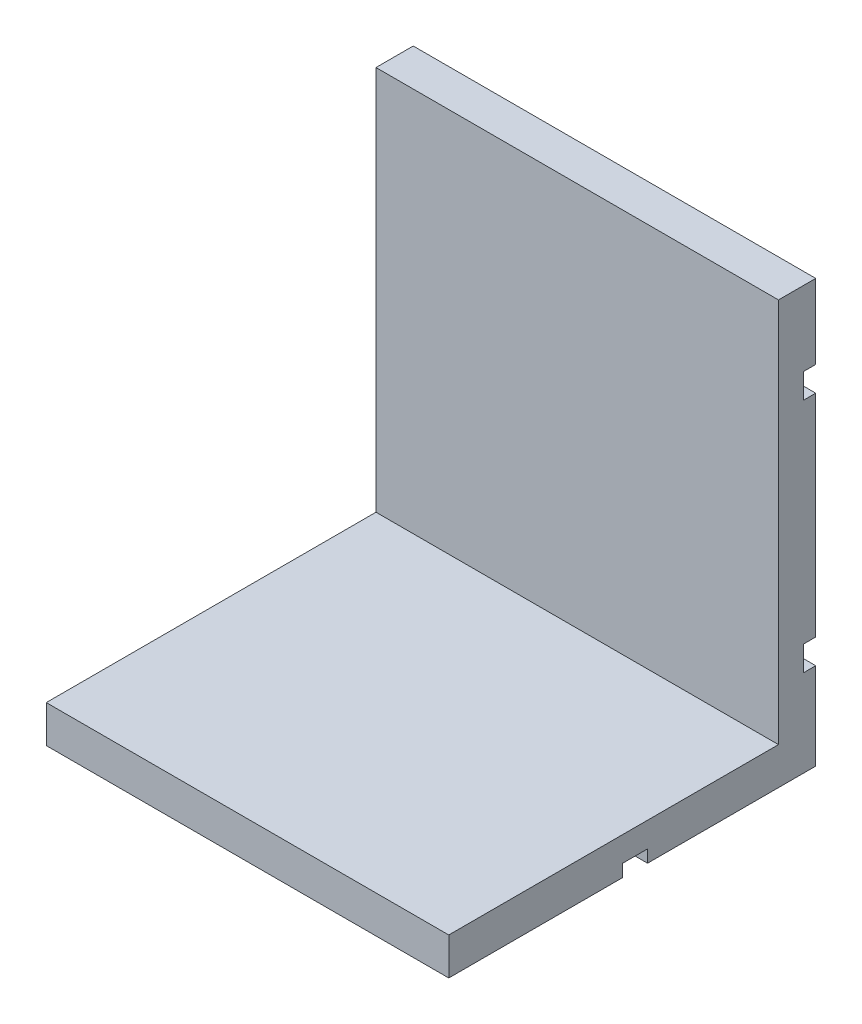
SolidWorks part; units mm, degrees
ref_plane "Front Plane" through (0, 0, 0) normal (0, 0, 1) x (1, 0, 0)
ref_plane "Top Plane" through (0, 0, 0) normal (0, 1, 0) x (1, 0, 0)
ref_plane "Right Plane" through (0, 0, 0) normal (1, 0, 0) x (0, 0, -1)
sketch "Sketch1" plane through (0, 0, 0) normal (1, 0, 0) x (0, 0, -1)
  line L0 (0, 0) -> (-7.77, 0)
  line L1 (-7.77, 0) -> (-7.77, 0.5)
  line L2 (-7.77, 0.5) -> (-6.77, 0.5)
  line L3 (-6.77, 0.5) -> (-6.77, 0)
  line L4 (-6.77, 0) -> (0, 0)
  line L5 (0, 0) -> (0, 3.5)
  line L6 (0, 3.5) -> (-0.5, 3.5)
  line L7 (-0.5, 3.5) -> (-0.5, 4.5)
  line L8 (-0.5, 4.5) -> (0, 4.5)
  line L9 (0, 4.5) -> (0, 13)
  line L10 (0, 13) -> (-0.5, 13)
  line L11 (-0.5, 13) -> (-0.5, 14)
  line L12 (-0.5, 14) -> (0, 14)
  line L13 (0, 14) -> (0, 17)
  line L14 (0, 17) -> (-1.5, 17)
  line L15 (-1.5, 17) -> (-1.5, 1.5)
  line L16 (-1.5, 1.5) -> (-14.77, 1.5)
  line L17 (-14.77, 1.5) -> (-14.77, 0)
  line L18 (-14.77, 0) -> (0, 0)
  dimension "D1" = 0.5
  dimension "D2" = 1
  dimension "D3" = 0.5
  dimension "D4" = 0.5
  dimension "D5" = 1
  dimension "D6" = 1
  dimension "D7" = 7
  dimension "D8" = 1.5
  dimension "D9" = 3.5
  dimension "D10" = 13
  dimension "D11" = 14.77
  dimension "D12" = 17
  dimension "D13" = 1.5
extrude "Boss-Extrude1" add sketch "Sketch1" along normal blind 16.2 contours L17 L18 L1 L2 L3 L0 L5 L6 L7 L8 L9 L10 L11 L12 L13 L14 L15 L16
